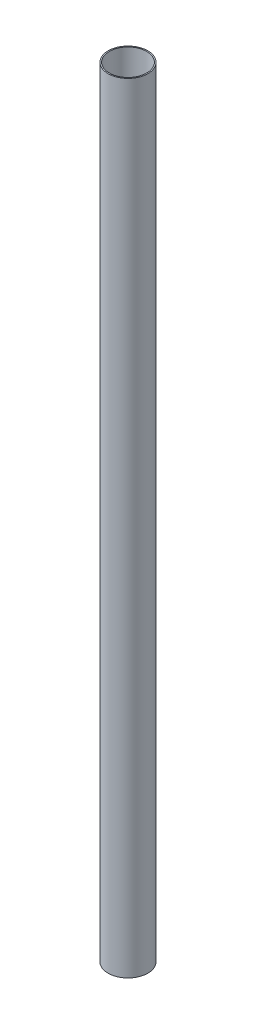
SolidWorks part; units mm, degrees
material "Chrome Stainless Steel"
ref_plane "Front Plane" through (0, 0, 0) normal (0, 0, 1) x (1, 0, 0)
ref_plane "Top Plane" through (0, 0, 0) normal (0, 1, 0) x (1, 0, 0)
ref_plane "Right Plane" through (0, 0, 0) normal (1, 0, 0) x (0, 0, -1)
sketch "Sketch1" plane through (0, 0, 0) normal (0, 1, 0) x (1, 0, 0)
  circle A0 centre (0, 0) radius 12
  circle A1 centre (0, 0) radius 12.75
  dimension "D1" = 24
  dimension "D2" = 25.5
extrude "Boss-Extrude1" add sketch "Sketch1" along normal blind 500
